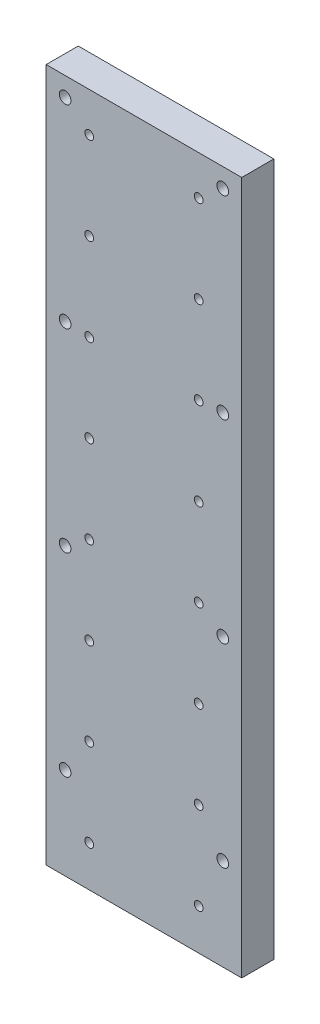
SolidWorks part; units mm, degrees
ref_plane "Płaszczyzna przednia" through (0, 0, 0) normal (0, 0, 1) x (1, 0, 0)
ref_plane "Płaszczyzna górna" through (0, 0, 0) normal (0, 1, 0) x (1, 0, 0)
ref_plane "Płaszczyzna prawa" through (0, 0, 0) normal (1, 0, 0) x (0, 0, -1)
sketch "Szkic1" plane through (0, 0, 0) normal (0, 0, 1) x (1, 0, 0)
  line L1 (67, -237.5) -> (-67, -237.5)
  line L2 (67, -237.5) -> (67, 237.5)
  line L3 (67, 237.5) -> (-67, 237.5)
  line L4 (-67, -237.5) -> (-67, 237.5)
  line L5 (67, -237.5) -> (-67, 237.5) construction
  line L6 (67, 237.5) -> (-67, -237.5) construction
  point P0 (0, 0)
  dimension "D1" = 475
  dimension "D2" = 134
extrude "Dodanie-wyciągnięcie1" add sketch "Szkic1" along normal blind 22
sketch "Szkic2" plane through (0, 0, 22) normal (0, 0, 1) x (1, 0, 0)
  line L0 (67, 237.5) -> (-67, 237.5) construction
  line L1 (-67, 237.5) -> (-67, -237.5) construction
  line L2 (67, -237.5) -> (67, 237.5) construction
  circle A0 centre (-54, 224.5) radius 4
  circle A1 centre (54, 224.5) radius 4
  dimension "D1" = 13
  dimension "D4" = 8
  dimension "D5" = 8
  dimension "D2" = 13
  dimension "D3" = 13
extrude "Wytnij-wyciągnięcie1" cut sketch "Szkic2" against normal blind 22
sketch "Szkic4" plane through (0, 0, 0) normal (0, 0, -1) x (-1, 0, 0)
  circle A0 centre (-54, 224.5) radius 6.5
  circle A1 centre (54, 224.5) radius 6.5
  dimension "D1" = 13
  dimension "D2" = 13
extrude "Wytnij-wyciągnięcie3" cut sketch "Szkic4" against normal blind 9
pattern_linear "Szyk liniowy3" count 4 spacing 133 along (0, -1, 0) of "Wytnij-wyciągnięcie3", "Wytnij-wyciągnięcie1"
sketch "Szkic5" plane through (0, 0, 0) normal (0, 0, -1) x (-1, 0, 0)
  line L0 (-67, 237.5) -> (67, 237.5) construction
  line L1 (67, 237.5) -> (67, -237.5) construction
  circle A7 centre (37.5, 210.5) radius 3
  point P12 (0, 0)
  dimension "D1" = 27
  dimension "D2" = 6
  dimension "D3" = 29.5
extrude "Wytnij-wyciągnięcie4" cut sketch "Szkic5" against normal blind 220
pattern_linear "Szyk liniowy5" count 8 spacing 60 along (0, -1, 0) count 2 spacing 75 along (1, 0, 0) of "Wytnij-wyciągnięcie4"
